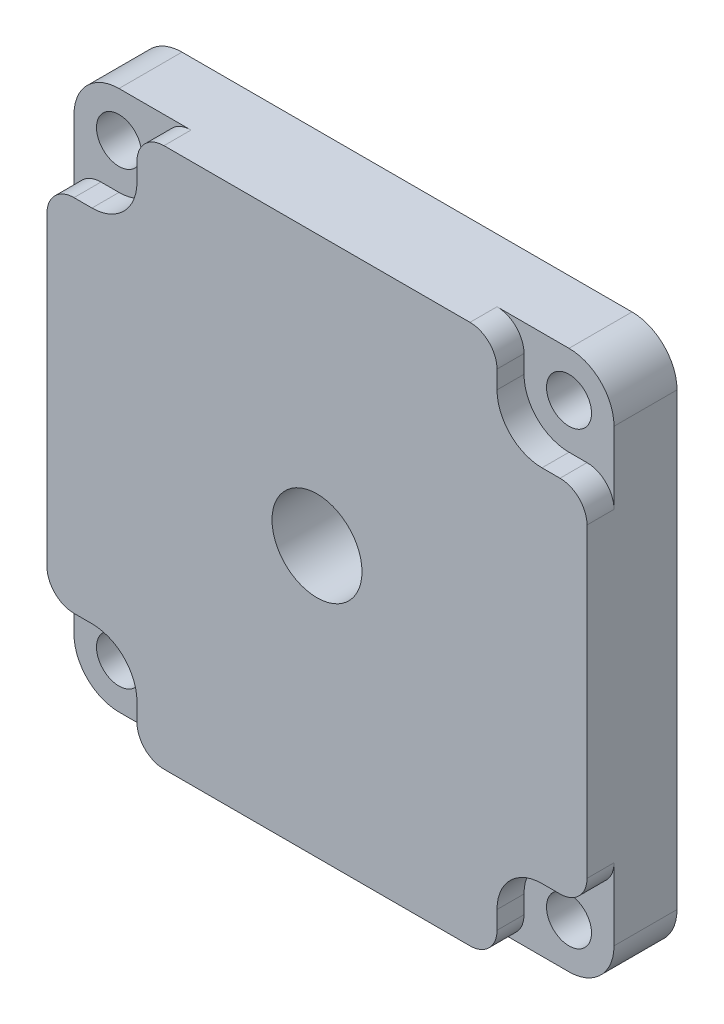
SolidWorks part; units mm, degrees
material "AISI 1020"
ref_plane "Ön Düzlem" through (0, 0, 0) normal (0, 0, 1) x (1, 0, 0)
ref_plane "Üst Düzlem" through (0, 0, 0) normal (0, 1, 0) x (1, 0, 0)
ref_plane "Sağ Düzlem" through (0, 0, 0) normal (1, 0, 0) x (0, 0, -1)
sketch "Çizim1" plane through (0, 0, 0) normal (0, 0, 1) x (1, 0, 0)
  line L0 (-28.7099, 29.8938) -> (21.2901, 29.8938)
  line L1 (26.2901, 24.8938) -> (26.2901, -25.1062)
  line L2 (21.2901, -30.1062) -> (-28.7099, -30.1062)
  line L3 (-33.7099, -25.1062) -> (-33.7099, 24.8938)
  arc A0 (21.2901, -30.1062) -> (26.2901, -25.1062) centre (21.2901, -25.1062) ccw
  arc A1 (-28.7099, -30.1062) -> (-33.7099, -25.1062) centre (-28.7099, -25.1062) cw
  arc A2 (26.2901, 24.8938) -> (21.2901, 29.8938) centre (21.2901, 24.8938) ccw
  arc A3 (-33.7099, 24.8938) -> (-28.7099, 29.8938) centre (-28.7099, 24.8938) cw
  circle A4 centre (-28.7099, 24.8938) radius 2.5
  circle A5 centre (21.2901, 24.8938) radius 2.5
  circle A6 centre (21.2901, -25.1062) radius 2.5
  circle A7 centre (-28.7099, -25.1062) radius 2.5
  point P6 (26.2901, -30.1062)
  point P11 (26.2901, 29.8938)
  point P14 (-33.7099, 29.8938)
  dimension "D3" = 5
  dimension "D4" = 5
  dimension "D5" = 5
  dimension "D6" = 5
  dimension "D7" = 5
  dimension "D1" = 60
  dimension "D2" = 60
extrude "Yükseklik-Ekstrüzyon1" add sketch "Çizim1" along normal blind 7
sketch "Çizim2" plane through (0, 0, 7) normal (0, 0, 1) x (1, 0, 0)
  line L0 (-20.7099, 29.8938) -> (13.2901, 29.8938)
  line L1 (21.2901, 29.8938) -> (-28.7099, 29.8938) construction
  line L2 (16.2901, 26.8938) -> (16.2901, 24.8938)
  line L3 (21.2901, 19.8938) -> (23.2901, 19.8938)
  line L4 (26.2901, -25.1062) -> (26.2901, 24.8938) construction
  line L5 (26.2901, 16.8938) -> (26.2901, -17.1062)
  line L6 (23.2901, -20.1062) -> (21.2901, -20.1062)
  line L7 (16.2901, -25.1062) -> (16.2901, -27.1062)
  line L8 (-28.7099, -30.1062) -> (21.2901, -30.1062) construction
  line L9 (13.2901, -30.1062) -> (-20.7099, -30.1062)
  line L10 (-23.7099, -27.1062) -> (-23.7099, -25.1062)
  line L11 (-28.7099, -20.1062) -> (-30.7099, -20.1062)
  line L12 (-33.7099, 24.8938) -> (-33.7099, -25.1062) construction
  line L13 (-33.7099, -17.1062) -> (-33.7099, 16.8938)
  line L14 (-30.7099, 19.8938) -> (-28.7099, 19.8938)
  line L15 (-23.7099, 24.8938) -> (-23.7099, 26.8938)
  line L18 (-33.7099, 19.8938) -> (-33.7099, -20.1062)
  arc A0 (-23.7099, -25.1062) -> (-28.7099, -20.1062) centre (-28.7099, -25.1062) ccw
  arc A1 (16.2901, -25.1062) -> (21.2901, -20.1062) centre (21.2901, -25.1062) cw
  arc A2 (21.2901, 19.8938) -> (16.2901, 24.8938) centre (21.2901, 24.8938) cw
  arc A3 (-28.7099, 19.8938) -> (-23.7099, 24.8938) centre (-28.7099, 24.8938) ccw
  arc A4 (23.2901, -20.1062) -> (26.2901, -17.1062) centre (23.2901, -17.1062) ccw
  arc A5 (13.2901, -30.1062) -> (16.2901, -27.1062) centre (13.2901, -27.1062) ccw
  arc A6 (-20.7099, -30.1062) -> (-23.7099, -27.1062) centre (-20.7099, -27.1062) cw
  arc A7 (-30.7099, -20.1062) -> (-33.7099, -17.1062) centre (-30.7099, -17.1062) cw
  arc A8 (-33.7099, 16.8938) -> (-30.7099, 19.8938) centre (-30.7099, 16.8938) cw
  arc A9 (26.2901, 16.8938) -> (23.2901, 19.8938) centre (23.2901, 16.8938) ccw
  arc A10 (16.2901, 26.8938) -> (13.2901, 29.8938) centre (13.2901, 26.8938) ccw
  arc A11 (-23.7099, 26.8938) -> (-20.7099, 29.8938) centre (-20.7099, 26.8938) cw
  point P17 (-23.7099, -20.1062)
  point P25 (16.2901, -20.1062)
  point P28 (16.2901, 19.8938)
  point P31 (-23.7099, 19.8938)
  point P34 (26.2901, -20.1062)
  point P37 (16.2901, -30.1062)
  point P40 (-23.7099, -30.1062)
  point P49 (26.2901, 19.8938)
  point P52 (16.2901, 29.8938)
  point P55 (-23.7099, 29.8938)
  line M4 (26.2901, -25.1062) -> (26.2901, 24.8938)
  line M6 (21.2901, 29.8938) -> (-28.7099, 29.8938)
  line M8 (-33.7099, 24.8938) -> (-33.7099, -25.1062)
  line M10 (-28.7099, -30.1062) -> (21.2901, -30.1062)
  dimension "D8" = 5
  dimension "D9" = 5
  dimension "D10" = 3
  dimension "D1" = 40
  dimension "D2" = 10
  dimension "D3" = 10
  dimension "D4" = 10
  dimension "D5" = 10
  dimension "D6" = 10
  dimension "D7" = 40
extrude "Yükseklik-Ekstrüzyon2" add sketch "Çizim2" along normal blind 3 contours A11 L15 A3 L14 A8 A7 L11 A0 L10 A6 A5 L7 A1 L6 A4 A9 L3 A2 L2 A10 M8 M10 M4 M6
sketch "Çizim4" plane through (0, 0, 0) normal (0, 0, -1) x (-1, 0, 0)
  line L4 (33.7099, 24.8938) -> (33.7099, -25.1062) construction
  line L5 (-21.2901, 29.8938) -> (28.7099, 29.8938) construction
  circle A0 centre (3.7099, -0.1062) radius 19
  dimension "D1" = 30
  dimension "D2" = 30
  dimension "D3" = 38
extrude "Yükseklik-Ekstrüzyon4" add sketch "Çizim4" along normal blind 1.2
fillet "Radyus1" radius 0.5 4 edges at (23.7901, -25.1062, 0) (-26.2099, -25.1062, 0) (-26.2099, 24.8938, 0) (23.7901, 24.8938, 0)
sketch "Çizim6" plane through (0, 0, -1.2) normal (0, 0, -1) x (-1, 0, 0)
  line L0 (33.7099, 24.8938) -> (33.7099, -25.1062) construction
  line L1 (-21.2901, 29.8938) -> (28.7099, 29.8938) construction
  circle A0 centre (3.7099, -0.1062) radius 5
  dimension "D1" = 30
  dimension "D2" = 30
  dimension "D3" = 10
extrude "Kes-Ekstrüzyon2" cut sketch "Çizim6" against normal through all
